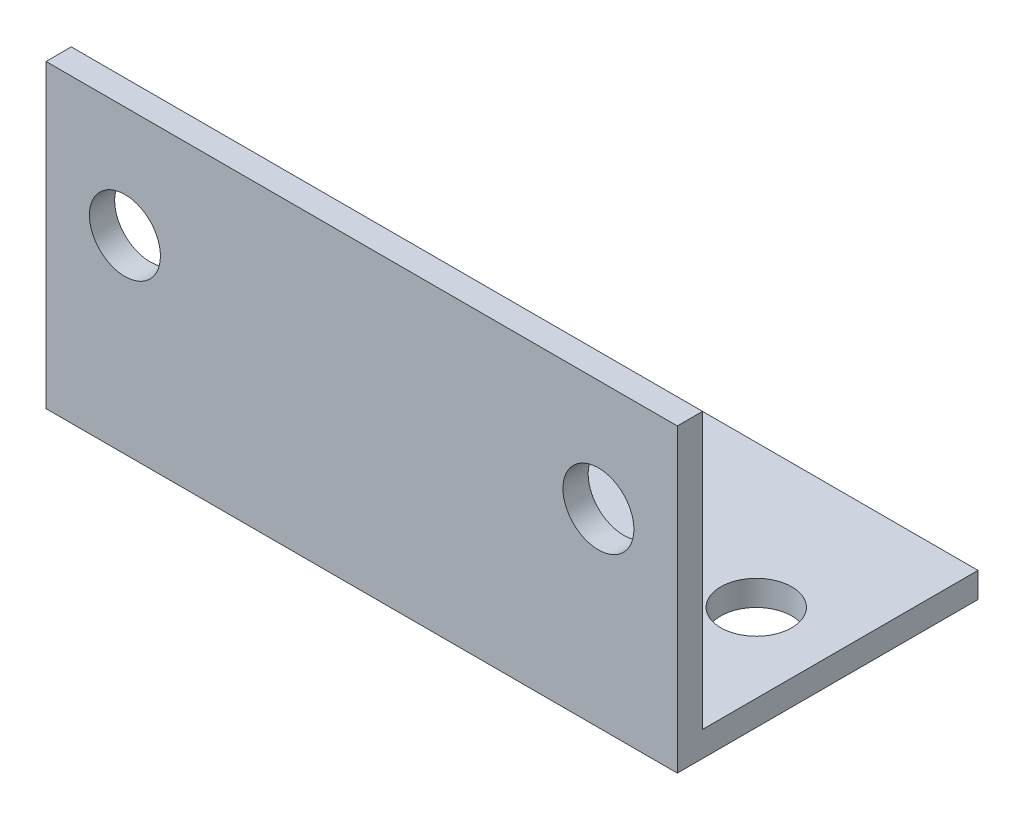
SolidWorks part; units mm, degrees
ref_plane "Front Plane" through (0, 0, 0) normal (0, 0, 1) x (1, 0, 0)
ref_plane "Top Plane" through (0, 0, 0) normal (0, 1, 0) x (1, 0, 0)
ref_plane "Right Plane" through (0, 0, 0) normal (1, 0, 0) x (0, 0, -1)
sketch "Sketch1" plane through (0, 0, 0) normal (1, 0, 0) x (0, 0, -1)
  line L0 (0, 0) -> (0, 19.05)
  line L1 (0, 19.05) -> (1.6, 19.05)
  line L2 (1.6, 19.05) -> (1.6, 1.6)
  line L3 (1.6, 1.6) -> (19.05, 1.6)
  line L4 (19.05, 1.6) -> (19.05, 0)
  line L5 (19.05, 0) -> (0, 0)
  dimension "D1" = 1.6
  dimension "D2" = 1.6
  dimension "D3" = 19.05
  dimension "D4" = 19.05
extrude "Boss-Extrude1" add sketch "Sketch1" along normal mid plane 40
hole_wizard "M4 Clearance Hole1" positions "Sketch4" profile "Sketch3" hole size "M4" standard "ANSI Metric" end condition through all
sketch "Sketch4" plane through (0, 0, 0) normal (0, 0, 1) x (1, 0, 0)
  line L0 (20, 0) -> (-20, 0) construction
  point P0 (-15, 12)
  point P2 (15, 12)
  dimension "D1" = 12
  dimension "D2" = 15
  dimension "D3" = 15
sketch "Sketch3" plane through (-15, 12, 0) normal (1, 0, 0) x (0, -1, 0)
  line L0 (0, 0) -> (0, 19.05)
  line L1 (0, 19.05) -> (2.25, 19.05)
  line L2 (2.25, 19.05) -> (2.25, 0)
  line L5 (2.25, 0) -> (0, 0)
  line L11 (0, -6.35) -> (0, 107.95) construction
  dimension "Thru Hole Dia." = 4.5
  dimension "Thru Hole Depth" = 19.05
hole_wizard "M4 Clearance Hole2" positions "Sketch8" profile "Sketch6" hole size "M4" standard "ANSI Metric" end condition through all
sketch "Sketch8" plane through (0, 0, 0) normal (0, -1, 0) x (-1, 0, 0)
  line L0 (-20, 0) -> (20, 0) construction
  point P0 (-15, 10)
  point P2 (15, 10)
  dimension "D1" = 15
  dimension "D2" = 10
  dimension "D3" = 15
sketch "Sketch6" plane through (15, 0, -10) normal (1, 0, 0) x (0, 0, -1)
  line L0 (0, 0) -> (0, 19.05)
  line L1 (0, 19.05) -> (2.25, 19.05)
  line L2 (2.25, 19.05) -> (2.25, 0)
  line L5 (2.25, 0) -> (0, 0)
  line L11 (0, -6.35) -> (0, 107.95) construction
  dimension "Thru Hole Dia." = 4.5
  dimension "Thru Hole Depth" = 19.05
